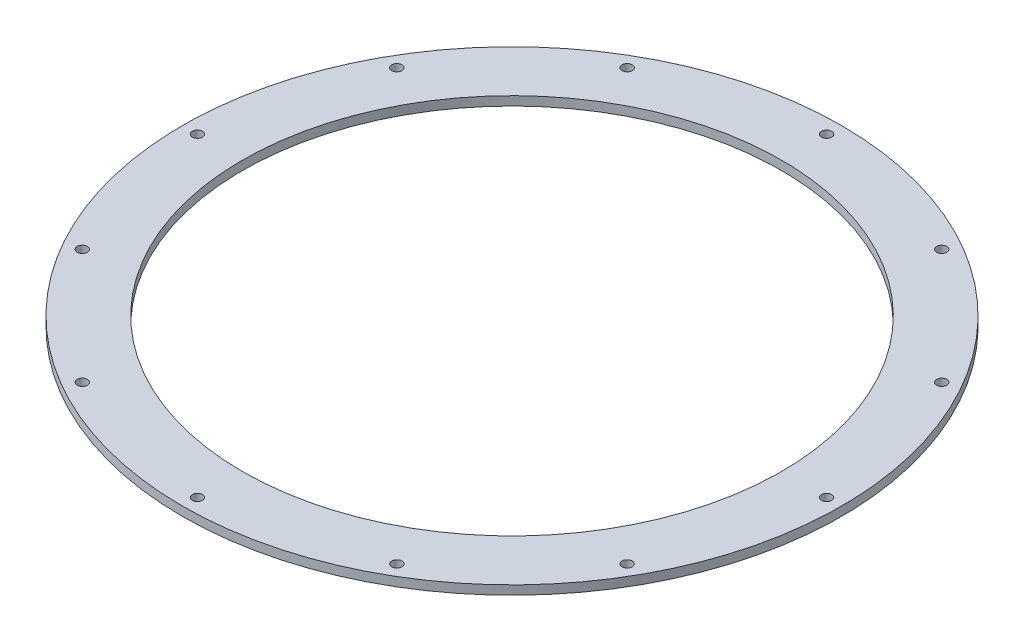
SolidWorks part; units mm, degrees
ref_plane "Front Plane" through (0, 0, 0) normal (0, 0, 1) x (1, 0, 0)
ref_plane "Top Plane" through (0, 0, 0) normal (0, 1, 0) x (1, 0, 0)
ref_plane "Right Plane" through (0, 0, 0) normal (1, 0, 0) x (0, 0, -1)
sketch "Sketch1" plane through (0, 0, 0) normal (0, 1, 0) x (1, 0, 0)
  circle A0 centre (0, 0) radius 90
  circle A1 centre (0, 0) radius 110
  circle A2 centre (0, 0) radius 105 construction
  circle A3 centre (0, 105) radius 1.7
  circle A4 centre (52.5, 90.9327) radius 1.7
  circle A5 centre (90.9327, 52.5) radius 1.7
  circle A6 centre (105, 0) radius 1.7
  circle A7 centre (90.9327, -52.5) radius 1.7
  circle A8 centre (52.5, -90.9327) radius 1.7
  circle A9 centre (0, -105) radius 1.7
  circle A10 centre (-52.5, -90.9327) radius 1.7
  circle A11 centre (-90.9327, -52.5) radius 1.7
  circle A12 centre (-105, 0) radius 1.7
  circle A13 centre (-90.9327, 52.5) radius 1.7
  circle A14 centre (-52.5, 90.9327) radius 1.7
  dimension "D1" = 180
  dimension "D2" = 220
  dimension "D3" = 210
  dimension "D4" = 3.4
  dimension "D5" = 12
extrude "Boss-Extrude1" add sketch "Sketch1" along normal blind 3 contours A1 A0
